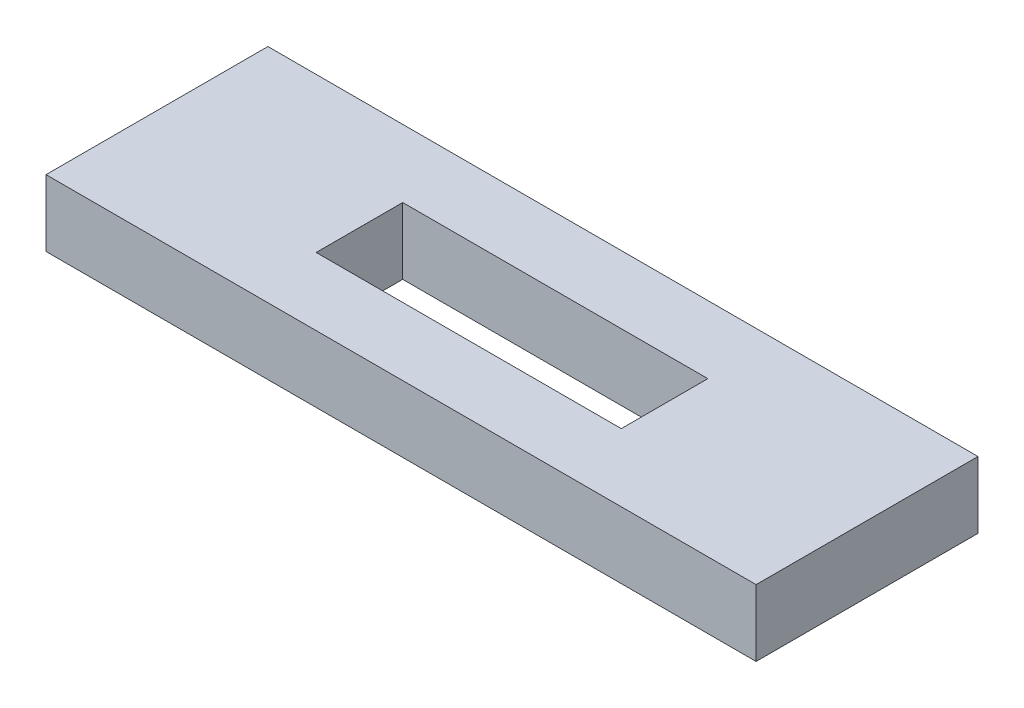
SolidWorks part; units mm, degrees
ref_plane "前基準面" through (0, 0, 0) normal (0, 0, 1) x (1, 0, 0)
ref_plane "上基準面" through (0, 0, 0) normal (0, 1, 0) x (1, 0, 0)
ref_plane "右基準面" through (0, 0, 0) normal (1, 0, 0) x (0, 0, -1)
sketch "草圖1" plane through (0, 0, 0) normal (0, 1, 0) x (1, 0, 0)
  line L1 (-16, -5) -> (16, -5)
  line L2 (-16, -5) -> (-16, 5)
  line L3 (-16, 5) -> (16, 5)
  line L4 (16, -5) -> (16, 5)
  line L5 (-16, -5) -> (16, 5) construction
  line L6 (-16, 5) -> (16, -5) construction
  point P0 (0, 0)
  dimension "D1" = 10
  dimension "D2" = 32
extrude "填料-伸長1" add sketch "草圖1" along normal blind 3
sketch "草圖2" plane through (0, 3, 0) normal (0, 1, 0) x (1, 0, 0)
  line L1 (-6.875, -1.95) -> (6.875, -1.95)
  line L2 (-6.875, -1.95) -> (-6.875, 1.95)
  line L3 (-6.875, 1.95) -> (6.875, 1.95)
  line L4 (6.875, -1.95) -> (6.875, 1.95)
  line L5 (-6.875, -1.95) -> (6.875, 1.95) construction
  line L6 (-6.875, 1.95) -> (6.875, -1.95) construction
  point P0 (0, 0)
  dimension "D1" = 3.9
  dimension "D2" = 13.75
extrude "除料-伸長1" cut sketch "草圖2" against normal through all
